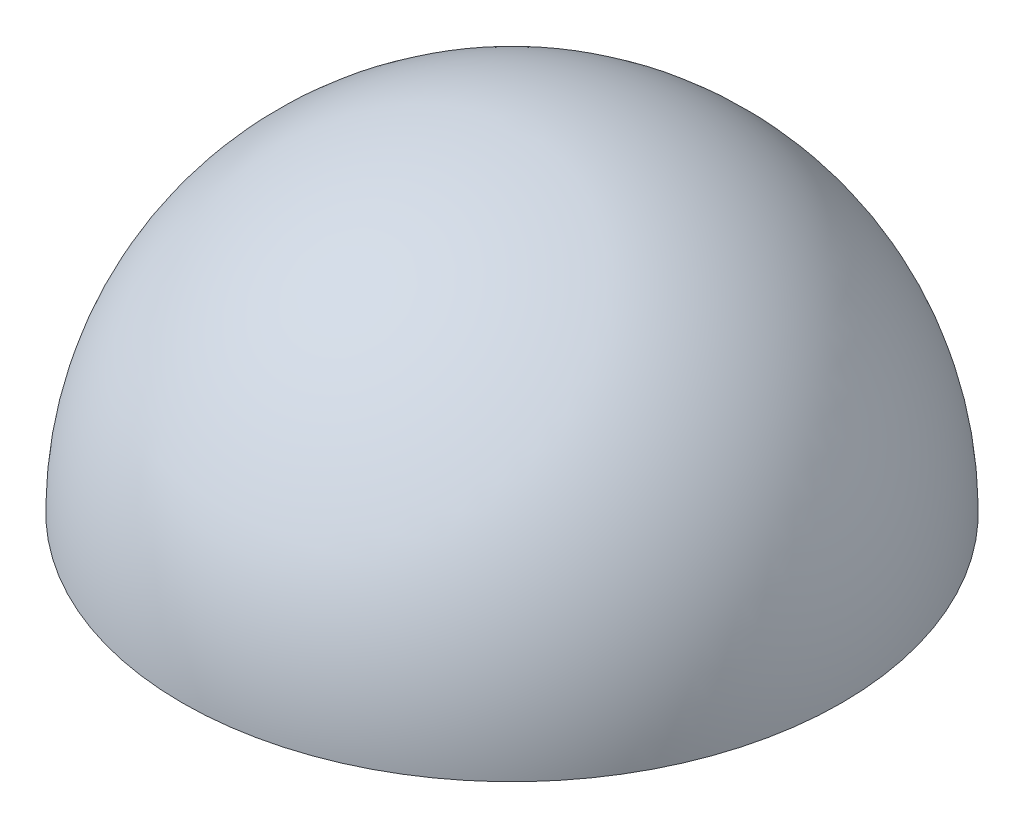
SolidWorks part; units mm, degrees
ref_plane "Front Plane" through (0, 0, 0) normal (0, 0, 1) x (1, 0, 0)
ref_plane "Top Plane" through (0, 0, 0) normal (0, 1, 0) x (1, 0, 0)
ref_plane "Right Plane" through (0, 0, 0) normal (1, 0, 0) x (0, 0, -1)
sketch "Sketch3" plane through (0, 0, 0) normal (1, 0, 0) x (0, 0, -1)
  line L0 (263.3528, -179.9323) -> (263.3528, -206.1427)
  line L1 (283.6728, -206.1427) -> (243.0328, -206.1427) construction
  line L2 (263.3528, -206.1427) -> (289.5632, -206.1427)
  arc A0 (289.5632, -206.1427) -> (263.3528, -179.9323) centre (263.3528, -206.1427) ccw
revolve "Revolve1" add sketch "Sketch3" angle 360 about L0
